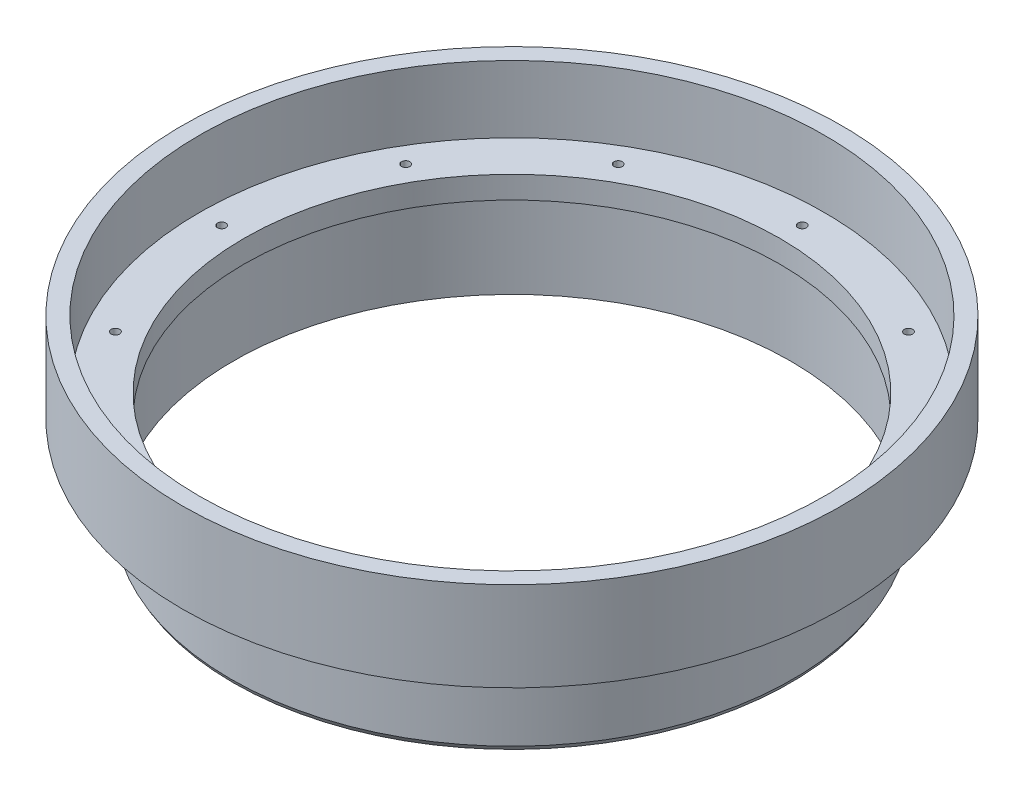
SolidWorks part; units mm, degrees
material "6061-T6 (SS)"
ref_plane "Front Plane" through (0, 0, 0) normal (0, 0, 1) x (1, 0, 0)
ref_plane "Top Plane" through (0, 0, 0) normal (0, 1, 0) x (1, 0, 0)
ref_plane "Right Plane" through (0, 0, 0) normal (1, 0, 0) x (0, 0, -1)
ref_axis "Axis1" through (0, 55, 0) along (0, -1, 0)
sketch "Cross Section" plane through (0, 0, 0) normal (0, 0, 1) x (1, 0, 0)
  line L0 (-38.1, 0) -> (-38.1, -3.175)
  line L1 (-38.1, -3.175) -> (-39.624, -3.175)
  line L2 (-39.624, -3.175) -> (-39.624, -15.875)
  line L3 (-39.624, -15.875) -> (-40.005, -15.2151)
  line L4 (0, -15.875) -> (-38.1, -15.875) construction
  line L5 (-40.005, -15.2151) -> (-40.005, -3.175)
  line L6 (-40.005, -3.175) -> (-46.863, -3.175)
  line L7 (-46.863, -3.175) -> (-46.863, 9.525)
  line L8 (-46.863, 9.525) -> (-44.45, 9.525)
  line L9 (-44.45, 9.525) -> (-44.45, 0)
  line L10 (-44.45, 0) -> (-38.1, 0)
  line L11 (-38.1, 0) -> (0, 0) construction
  line L12 (0, 55) -> (0, -55) construction
  line L14 (-44.45, 1.5875) -> (-44.45, 3.175) construction
  dimension "D1" = 1.524
  dimension "D3" = 0.381
  dimension "D4" = 30
  dimension "D5" = 6.858
  dimension "D6" = 12.7
  dimension "D9" = 3.175
  dimension "D8" = 38.1
revolve "Main" add sketch "Cross Section" angle 360 about axis through (0, 55, 0) along (0, -1, 0)
sketch "Hole Location" plane through (0, 0, 0) normal (0, 1, 0) x (1, 0, 0)
  line L0 (0, 0) -> (-41.275, 0) construction
  circle A0 centre (0, 0) radius 41.275 construction
  dimension "D1" = 82.55
hole_wizard "#0-80 Tapped Hole1" positions "Sketch5" profile "Sketch7" tap size "#0-80" standard "ANSI Inch"
sketch "Sketch5" plane through (0, 0, 0) normal (0, 1, 0) x (1, 0, 0)
  point P0 (-41.275, 0)
sketch "Sketch7" plane through (-41.275, 0, 0) normal (1, 0, 0) x (0, 0, 1)
  line L0 (0, 0) -> (0, 3.5329)
  line L1 (0, 3.5329) -> (0.5956, 3.175)
  line L2 (0.5956, 3.175) -> (0.5956, 0)
  line L5 (0.5956, 0) -> (0, 0)
  line L10 (0, 3.5329) -> (-0.5956, 3.175) construction
  line L11 (0, -6.35) -> (0, 107.95) construction
  dimension "Tap Drill Dia." = 1.1913
  dimension "Tap Drill Depth" = 3.175
  dimension "Drill Angle" = 118
cosmetic thread "Hole Thread1" parameters "D1"=3.048, "D2"=1.524
pattern_circular "Screw Holes" count 12 over 360 about axis through (0, 0, 0) along (0, 1, 0) of "#0-80 Tapped Hole1"
equation "\"D8@Cross Section\"=\"TANK DIAMETER@Cryo Tank.Assembly\"/2"
equation "\"D1@Hole Location\"=\"TANK DIAMETER@Cryo Tank.Assembly\"+\"GASKET SEAT THICKNESS@Cryo Tank.Assembly\""
equation "\"D1@Cross Section\"=\"LINER THICKNESS@Cryo Tank.Assembly\""
equation "\"D3@Cross Section\"=\"ALUMINUM LAP THICKNESS@Cryo Tank.Assembly\""
equation "\"D5@Cross Section\"=2*\"CF THICKNESS@Cryo Tank.Assembly\"+\"NOMEX THICKNESS@Cryo Tank.Assembly\""
